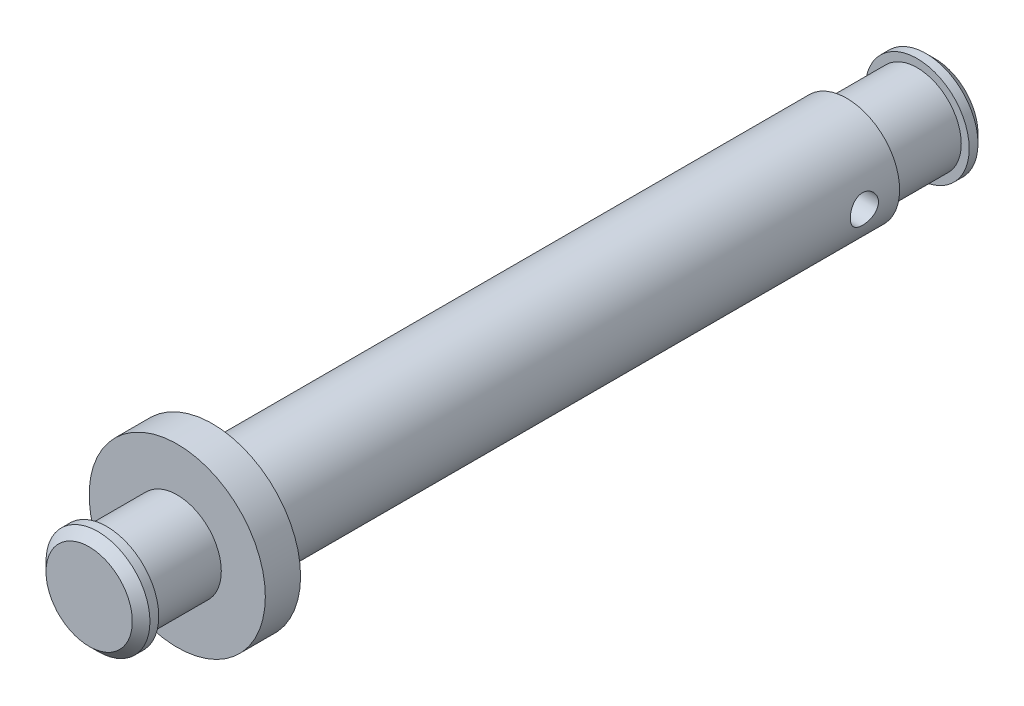
SolidWorks part; units mm, degrees
material "10"
ref_plane "Спереди" through (0, 0, 0) normal (0, 0, 1) x (1, 0, 0)
ref_plane "Сверху" through (0, 0, 0) normal (0, 1, 0) x (1, 0, 0)
ref_plane "Справа" through (0, 0, 0) normal (1, 0, 0) x (0, 0, -1)
sketch "Эскиз1" plane through (0, 0, 0) normal (1, 0, 0) x (0, 0, -1)
  line L0 (0, 0) -> (49.4156, 0) construction
  line L1 (0, 2.5) -> (0, 5)
  line L2 (0, 5) -> (2, 5)
  line L3 (2, 5) -> (2, 3)
  line L4 (2, 3) -> (38, 3)
  line L5 (43, 2.95) -> (43, 0)
  line L6 (43, 0) -> (0, 0)
  line L7 (0, 0) -> (-5, 0)
  line L8 (-5, 0) -> (-5, 2.95)
  line L9 (-5, 2.95) -> (-4, 2.95)
  line L10 (-4, 2.95) -> (-4, 2.5)
  line L11 (-4, 2.5) -> (0, 2.5)
  line L12 (0, 0) -> (0, 2.5) construction
  line L13 (38, 3) -> (38, 2.5)
  line L14 (38, 2.5) -> (42, 2.5)
  line L15 (42, 2.5) -> (42, 2.95)
  line L16 (42, 2.95) -> (43, 2.95)
  dimension "D1" = 10
  dimension "D2" = 2
  dimension "D3" = 41
  dimension "D4" = 6
  dimension "D5" = 5.9
  dimension "D6" = 5
  dimension "D7" = 5
  dimension "D8" = 1
  dimension "D9" = 1
  dimension "D10" = 5
  dimension "D11" = 5
  dimension "D12" = 5.9
revolve "Повернуть1" add sketch "Эскиз1" angle 360 about L0
sketch "Эскиз2" plane through (0, 0, 0) normal (1, 0, 0) x (0, 0, -1)
  line L0 (0, 0) -> (36, 0) construction
  line L1 (2, -5) -> (2, 5) construction
  circle A0 centre (36, 0) radius 0.8
  dimension "D1" = 1.6
  dimension "D2" = 34
extrude "Вытянуть1" cut sketch "Эскиз2" against normal mid plane 20
chamfer "Фаска1" distance 0.5 angle 45 2 edges at (2.95, 0, 5) (2.95, 0, -43)
